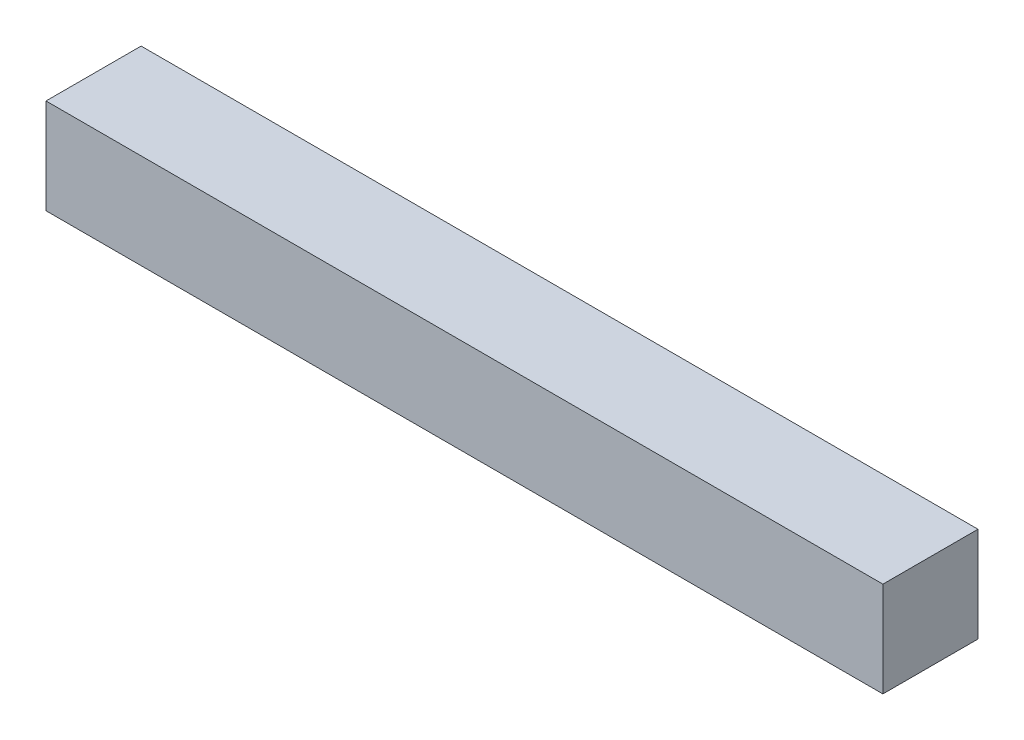
SolidWorks part; units mm, degrees
ref_plane "Front Plane" through (0, 0, 0) normal (0, 0, 1) x (1, 0, 0)
ref_plane "Top Plane" through (0, 0, 0) normal (0, 1, 0) x (1, 0, 0)
ref_plane "Right Plane" through (0, 0, 0) normal (1, 0, 0) x (0, 0, -1)
sketch "Sketch1" plane through (0, 0, 0) normal (0, 0, 1) x (1, 0, 0)
  line L1 (-220, -25) -> (220, -25)
  line L2 (-220, -25) -> (-220, 25)
  line L3 (-220, 25) -> (220, 25)
  line L4 (220, -25) -> (220, 25)
  line L5 (-220, -25) -> (220, 25) construction
  line L6 (-220, 25) -> (220, -25) construction
  point P0 (0, 0)
  dimension "D1" = 440
  dimension "D2" = 50
extrude "Boss-Extrude1" add sketch "Sketch1" along normal blind 50
